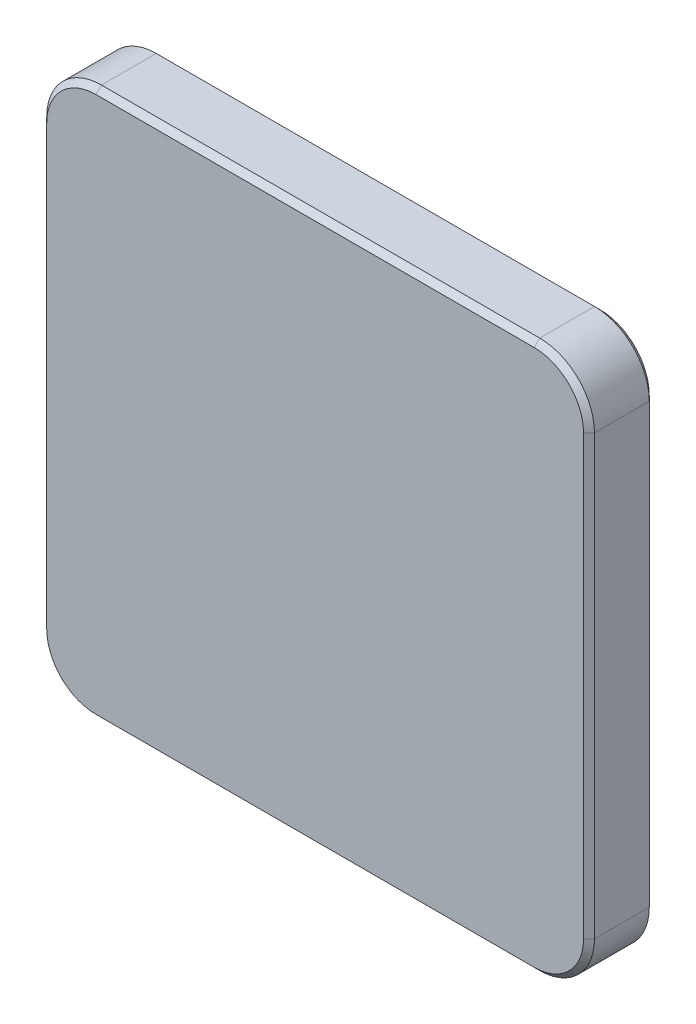
SolidWorks part; units mm, degrees
ref_plane "Front Plane" through (0, 0, 0) normal (0, 0, 1) x (1, 0, 0)
ref_plane "Top Plane" through (0, 0, 0) normal (0, 1, 0) x (1, 0, 0)
ref_plane "Right Plane" through (0, 0, 0) normal (1, 0, 0) x (0, 0, -1)
sketch "Sketch1" plane through (0, 0, 0) normal (0, 0, 1) x (1, 0, 0)
  line L1 (-50, -50) -> (50, -50)
  line L2 (-50, -50) -> (-50, 50)
  line L3 (-50, 50) -> (50, 50)
  line L4 (50, -50) -> (50, 50)
  line L5 (-50, -50) -> (50, 50) construction
  line L6 (-50, 50) -> (50, -50) construction
  point P0 (0, 0)
  dimension "D1" = 100
extrude "Boss-Extrude1" add sketch "Sketch1" along normal blind 12
fillet "Fillet1" radius 10 4 edges at (-50, 50, 6) (-50, -50, 6) (50, -50, 6) (50, 50, 6)
chamfer "Chamfer1" distance 1 angle 45 8 edges at (-47.0711, -47.0711, 0) (0, -50, 0) (47.0711, -47.0711, 0) (50, 0, 0) (47.0711, 47.0711, 0) (0, 50, 0) (-47.0711, 47.0711, 0) (-50, 0, 0)
chamfer "Chamfer2" distance 1 angle 45 8 edges at (47.0711, 47.0711, 12) (50, 0, 12) (47.0711, -47.0711, 12) (0, -50, 12) (-47.0711, -47.0711, 12) (-50, 0, 12) (-47.0711, 47.0711, 12) (0, 50, 12)
